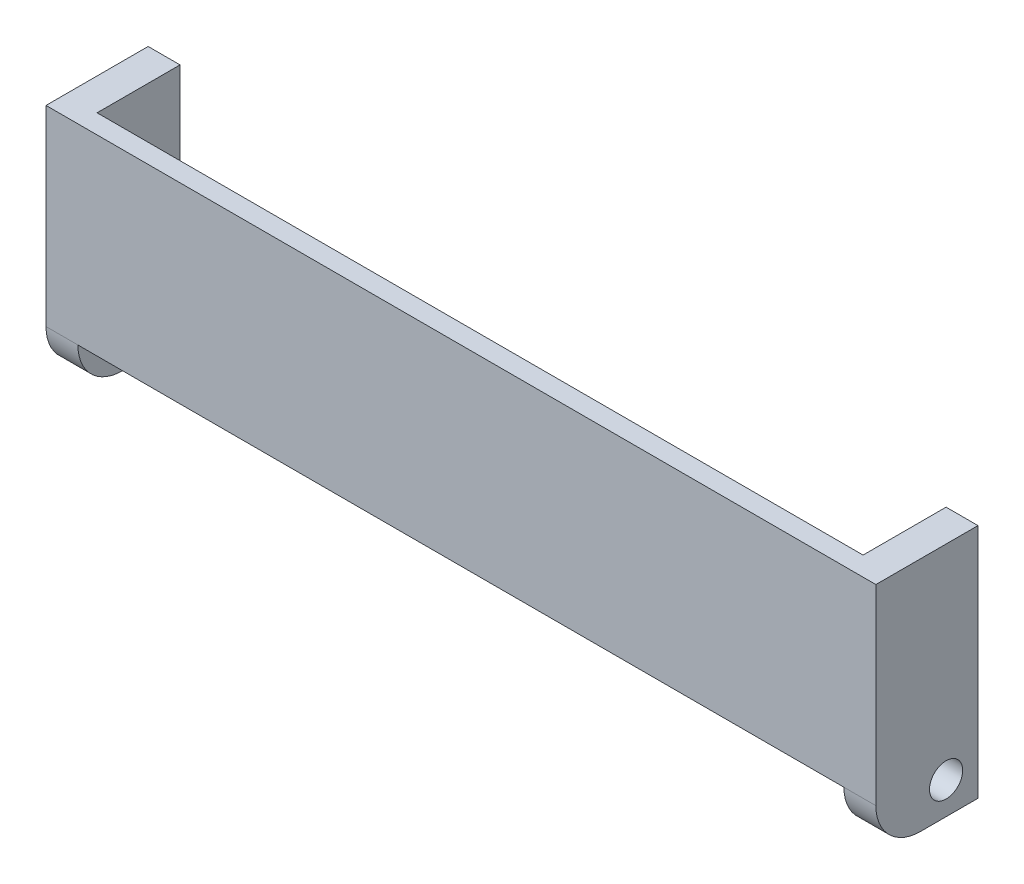
SolidWorks part; units mm, degrees
ref_plane "Plan de face" through (0, 0, 0) normal (0, 0, 1) x (1, 0, 0)
ref_plane "Plan de dessus" through (0, 0, 0) normal (0, 1, 0) x (1, 0, 0)
ref_plane "Plan de droite" through (0, 0, 0) normal (1, 0, 0) x (0, 0, -1)
sketch "Esquisse1" plane through (0, 0, 0) normal (0, 0, 1) x (1, 0, 0)
  line L1 (0, 0) -> (5, 0)
  line L2 (0, 0) -> (0, -40)
  line L3 (0, -40) -> (5, -40)
  line L4 (5, 0) -> (5, -40)
  dimension "D1" = 5
  dimension "D2" = 40
extrude "Boss.-Extru.1" add sketch "Esquisse1" along normal blind 10
sketch "Esquisse2" plane through (5, 0, 0) normal (1, 0, 0) x (0, 0, -1)
  line L0 (-10, -40) -> (0, -40) construction
  circle A0 centre (-5, -35) radius 2.6
  point P5 (-5, -40)
  dimension "D1" = 5.2
  dimension "D2" = 5
extrude "Enlèv. mat.-Extru.1" cut sketch "Esquisse2" against normal blind 10
sketch "Esquisse3" plane through (0, 0, 10) normal (0, 0, 1) x (1, 0, 0)
  line L1 (0, 0) -> (5, 0)
  line L2 (0, 0) -> (0, -40)
  line L3 (0, -40) -> (5, -40)
  line L4 (5, 0) -> (5, -40)
extrude "Boss.-Extru.2" add sketch "Esquisse3" along normal blind 6
fillet "Congé1" radius 7 1 edges at (2.5, -40, 16)
sketch "Esquisse6" plane through (0, 0, 0) normal (-1, 0, 0) x (0, 0, 1)
  line L0 (13, 0) -> (16, 0)
  line L1 (16, 0) -> (0, 0) construction
  line L2 (16, 0) -> (16, -33)
  line L3 (16, -33) -> (13, -33)
  line L4 (13, -33) -> (13, 0)
  dimension "D1" = 3
extrude "Boss.-Extru.4" add sketch "Esquisse6" along normal blind 120
sketch "Esquisse8" plane through (-120, 0, 0) normal (-1, 0, 0) x (0, 0, 1)
  line L0 (16, 0) -> (0, 0)
  line L1 (0, 0) -> (0, -40)
  line L2 (0, -40) -> (9, -40)
  line L3 (16, 0) -> (16, -33)
  arc A0 (16, -33) -> (9, -40) centre (9, -33) cw
  circle A1 centre (5, -35) radius 2.6
  dimension "D1" = 5.2
extrude "Boss.-Extru.5" add sketch "Esquisse8" along normal blind 5
sketch "Esquisse9" plane through (0, 0, 0) normal (0, 0, 1) x (1, 0, 0)
  line L0 (-125, 0) -> (-125, -3)
  line L1 (-125, -33) -> (-125, 0) construction
  line L2 (-125, -3) -> (5, -3)
  line L3 (5, -33) -> (5, 0) construction
  line L4 (5, -3) -> (5, 0)
  line L5 (5, 0) -> (-125, 0)
  dimension "D1" = 3
extrude "Enlèv. mat.-Extru.2" cut sketch "Esquisse9" along normal blind 20
